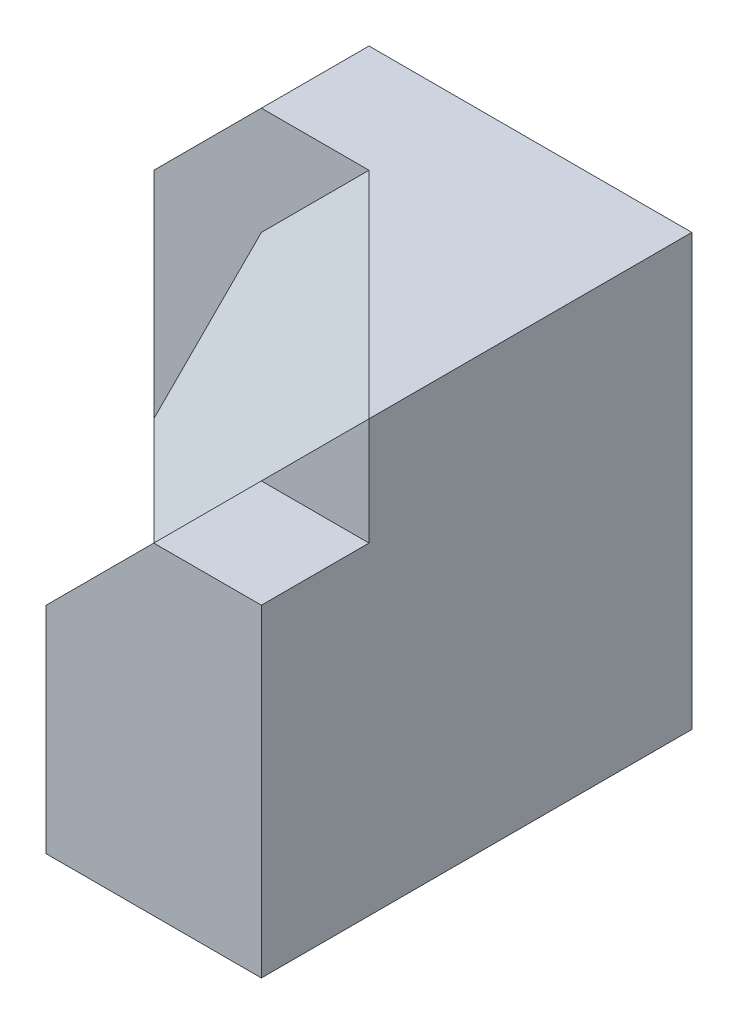
SolidWorks part; units mm, degrees
ref_plane "Front Plane" through (0, 0, 0) normal (0, 0, 1) x (1, 0, 0)
ref_plane "Top Plane" through (0, 0, 0) normal (0, 1, 0) x (1, 0, 0)
ref_plane "Right Plane" through (0, 0, 0) normal (1, 0, 0) x (0, 0, -1)
sketch "Sketch1" plane through (0, 0, 0) normal (0, 1, 0) x (1, 0, 0)
  line L0 (-23.6564, 13.9097) -> (-8.6564, 13.9097)
  line L1 (-8.6564, 13.9097) -> (-8.6564, -1.0903)
  line L2 (-8.6564, -1.0903) -> (-18.6564, 8.9097)
  line L3 (-18.6564, 8.9097) -> (-23.6564, 8.9097)
  line L4 (-23.6564, 8.9097) -> (-23.6564, 13.9097)
  dimension "D1" = 15
  dimension "D2" = 15
  dimension "D3" = 5
  dimension "D4" = 5
extrude "Boss-Extrude1" add sketch "Sketch1" along normal blind 20
sketch "Sketch2" plane through (-23.6564, 0, 0) normal (-1, 0, 0) x (0, 0, 1)
  line L1 (-13.9097, 0) -> (-8.9097, 0)
  line L2 (-13.9097, 0) -> (-13.9097, 20)
  line L3 (-13.9097, 20) -> (-8.9097, 20)
  line L4 (-8.9097, 0) -> (-8.9097, 20)
extrude "Boss-Extrude2" add sketch "Sketch2" along normal blind 5
sketch "Sketch3" plane through (0, 0, -8.9097) normal (0, 0, 1) x (1, 0, 0)
  line L0 (-23.6564, 20) -> (-28.6564, 15)
  line L1 (-28.6564, 20) -> (-18.6564, 20) construction
  line L2 (-28.6564, 0) -> (-28.6564, 20) construction
  line L3 (-28.6564, 15) -> (-28.6564, 20)
  line L4 (-28.6564, 20) -> (-23.6564, 20)
  dimension "D1" = 5
  dimension "D2" = 5
extrude "Cut-Extrude1" cut sketch "Sketch3" against normal blind 5
sketch "Sketch4" plane through (0, 0, -8.9097) normal (0, 0, 1) x (1, 0, 0)
  line L1 (-28.6564, 5) -> (-23.6564, 5)
  line L2 (-28.6564, 0) -> (-28.6564, 15) construction
  line L3 (-23.6564, 5) -> (-23.6564, 0)
  line L4 (-28.6564, 0) -> (-18.6564, 0) construction
  line L5 (-23.6564, 0) -> (-28.6564, 0)
  line L6 (-28.6564, 0) -> (-28.6564, 5)
  dimension "D1" = 5
  dimension "D2" = 5
extrude "Boss-Extrude3" add sketch "Sketch4" along normal blind 5
sketch "Sketch5" plane through (0, 5, 0) normal (0, 1, 0) x (1, 0, 0)
  line L0 (-28.6564, 8.9097) -> (-23.6564, 3.9097)
  line L1 (-23.6564, 3.9097) -> (-28.6564, 3.9097)
  line L2 (-28.6564, 3.9097) -> (-28.6564, 8.9097)
extrude "Cut-Extrude2" cut sketch "Sketch5" against normal blind 5
ref_plane "Plane1" through (0, 0, 0) normal (0, -1, 0) x (-1, 0, 0)
sketch "Sketch6" plane through (0, 0, 0) normal (0, -1, 0) x (-1, 0, 0)
  line L0 (18.6564, -1.0903) -> (23.6564, 3.9097)
  line L2 (18.6564, -1.0903) -> (8.6564, -1.0903)
  line L3 (8.6564, -1.0903) -> (18.6564, 8.9097)
  line L4 (18.6564, 8.9097) -> (23.6564, 8.9097)
  line L5 (23.6564, 3.9097) -> (23.6564, 8.9097)
  dimension "D1" = 10
extrude "Boss-Extrude4" add sketch "Sketch6" against normal blind 20
sketch3d "3DSketch1"
  line L0 (-23.6564, 20, -8.9097) -> (-23.6564, 5, -8.9097) construction
  line L1 (-23.6564, 20, -3.9097) -> (-23.6564, 5, -3.9097) construction
  line L2 (-18.6564, 20, 1.0903) -> (-18.6564, 0, 1.0903) construction
  line L3 (-8.6564, 20, -13.9097) -> (-23.6564, 20, -13.9097) construction
  line L4 (-23.6564, 20, -13.9097) -> (-23.6564, 20, -8.9097) construction
  line L5 (-18.6564, 20, 1.0903) -> (-23.6564, 20, -3.9097) construction
  line L6 (-8.6564, 20, 1.0903) -> (-18.6564, 20, 1.0903) construction
  line L7 (-23.6564, 20, -3.9097) -> (-23.6564, 20, -8.9097) construction
  line L8 (-8.6564, 20, 1.0903) -> (-18.6564, 20, -8.9097)
  line L9 (-8.6564, 20, 1.0903) -> (-18.6564, 10, 1.0903)
  line L10 (-18.6564, 10, 1.0903) -> (-23.6564, 10, -3.9097)
  line L11 (-23.6564, 10, -3.9097) -> (-23.6564, 15, -8.9097)
  line L12 (-18.6564, 20, -8.9097) -> (-23.6564, 15, -8.9097)
  point P0 (-18.6564, 20, -8.9097)
  point P1 (-23.6564, 15, -8.9097)
  point P2 (-23.6564, 10, -3.9097)
  point P5 (-18.6564, 10, 1.0903)
  point P8 (-8.6564, 20, 1.0903)
  dimension "D1" = 5
  dimension "D2" = 5
  dimension "D3" = 10
  dimension "D4" = 10
  dimension "D5" = 5
extrude "Cut-Extrude3" cut sketch "3DSketch1" along direction (0, -1, 0) on the side of the normal blind 20
sketch "Sketch7" plane through (0, 0, 1.0903) normal (0, 0, 1) x (1, 0, 0)
  line L0 (-8.6564, 15) -> (-13.6564, 15)
  line L1 (-8.6564, 20) -> (-8.6564, 0) construction
  line L2 (-13.6564, 15) -> (-18.6564, 10)
  line L3 (-18.6564, 10) -> (-18.6564, 0)
  line L4 (-18.6564, 0) -> (-8.6564, 0)
  line L5 (-8.6564, 0) -> (-8.6564, 15)
  dimension "D1" = 5
  dimension "D2" = 15
  dimension "D3" = 10
  dimension "D4" = 10
extrude "Boss-Extrude5" add sketch "Sketch7" along normal blind 5
